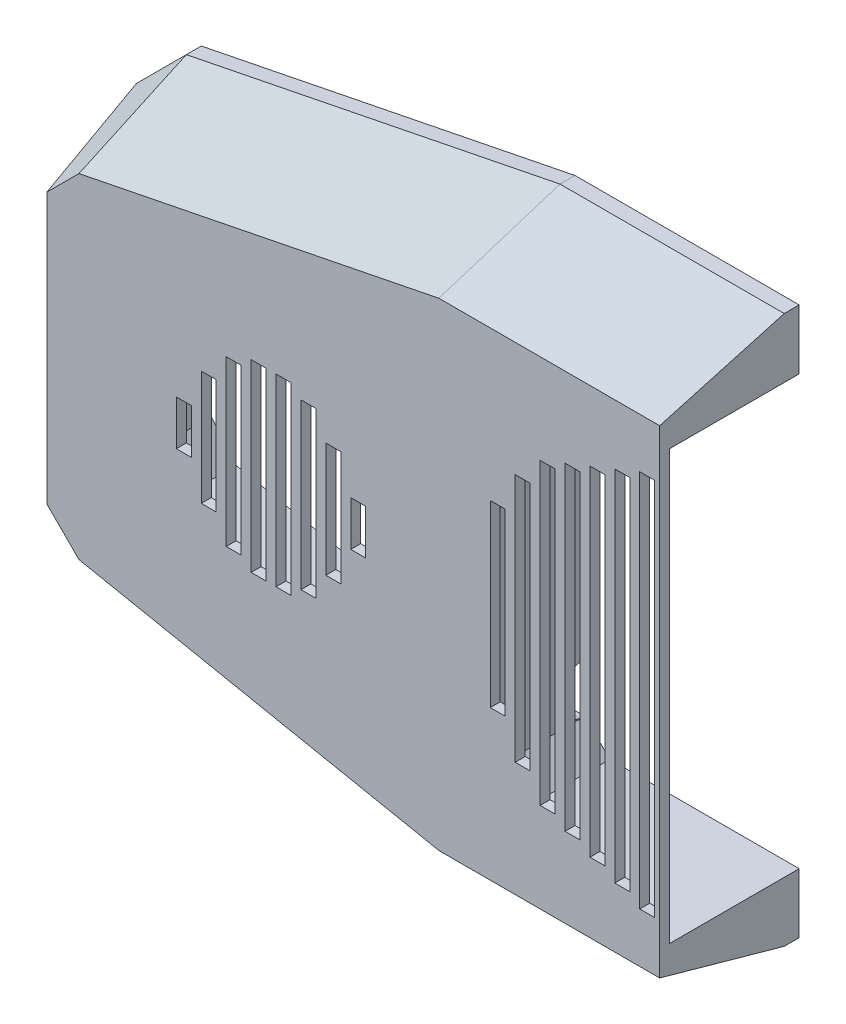
SolidWorks part; units mm, degrees
ref_plane "Plano frontal" through (0, 0, 0) normal (0, 0, 1) x (1, 0, 0)
ref_plane "Plano superior" through (0, 0, 0) normal (0, 1, 0) x (1, 0, 0)
ref_plane "Plano direito" through (0, 0, 0) normal (1, 0, 0) x (0, 0, -1)
sketch "Esboço1" plane through (0, 0, 0) normal (0, 0, 1) x (1, 0, 0)
  line L0 (-120, 30) -> (-45, 45)
  line L1 (-40, 40) -> (40, 40)
  line L2 (-40, 40) -> (-40, -40)
  line L3 (-40, -40) -> (40, -40)
  line L4 (40, 40) -> (40, -40)
  line L6 (-45, 45) -> (-45, 43)
  line L7 (-120, 30) -> (-120, 28)
  line L8 (-40, 30) -> (-40, -30)
  line L9 (-120, -30) -> (-120, -28)
  line L10 (-120, 30) -> (-120, -30)
  line L11 (-45, -43) -> (-120, -28)
  line L12 (40, 30) -> (40, -30)
  line L13 (-120, 28) -> (-45, 43)
  line L14 (120, 30) -> (120, -30)
  line L15 (-45, 45) -> (45, 45)
  line L17 (-45, -45) -> (45, -45)
  line L18 (45, 45) -> (45, -45)
  line L19 (45, -45) -> (45, -43)
  line L21 (-120, -30) -> (-120, 30)
  line L22 (-120, -30) -> (-45, -45)
  line L24 (45, 45) -> (120, 30)
  line L25 (45, -45) -> (120, -30)
  line L27 (-120, -30) -> (-120, 30)
  line L28 (-120, -30) -> (-120, 30)
  line L29 (120, -30) -> (120, -28)
  line L30 (120, 30) -> (120, 28)
  line L31 (45, 45) -> (45, 43)
  line L32 (45, 43) -> (120, 28)
  line L33 (45, -43) -> (120, -28)
  line L36 (120, 30) -> (120, -30)
  line L39 (-45, 45) -> (45, 45)
  line L40 (-45, 45) -> (-45, 43)
  line L41 (-43, 43) -> (43, 43)
  line L42 (45, 45) -> (45, 43)
  line L43 (-45, -45) -> (45, -45)
  line L45 (-43, 43) -> (-43, -43)
  line L46 (45, -45) -> (45, -43)
  line L47 (-45, -43) -> (-43, -43)
  line L48 (-45, -43) -> (-45, 43)
  line L49 (-45, 43) -> (-43, 43)
  line L50 (-43, -43) -> (-43, 43)
  line L51 (45, 43) -> (43, 43)
  line L52 (45, 43) -> (45, -43)
  line L53 (45, -43) -> (43, -43)
  line L54 (43, 43) -> (43, -43)
  line L56 (-43, -43) -> (43, -43)
  line L57 (43, 43) -> (43, -43)
  point P0 (0, 0)
  point P14 (0, 0)
  dimension "D3" = 2
extrude "Ressalto-extrusão3" add sketch "Esboço1" along normal blind 25
sketch "Esboço6" plane through (0, 0, 0) normal (0, 0, 1) x (1, 0, 0)
  line L0 (-120, -28) -> (-120, 28)
  line L1 (-120, 28) -> (-118, 28.4)
  line L2 (-120, 28) -> (-45, 43) construction
  line L3 (-118, 28.4) -> (-118, -28.4)
  line L4 (-45, -43) -> (-120, -28) construction
  line L5 (-118, -28.4) -> (-120, -28)
  line L6 (120, 28) -> (120, -28)
  line L7 (120, -28) -> (118, -28.4)
  line L8 (45, -43) -> (120, -28) construction
  line L9 (118, -28.4) -> (118, 28.4)
  line L10 (118, 28.4) -> (120, 28)
  dimension "D1" = 2
extrude "Ressalto-extrusão16" add sketch "Esboço6" along normal blind 25
sketch "Esboço7" plane through (0, 0, 0) normal (0, 0, 1) x (1, 0, 0)
  line L0 (-120, 40) -> (-45, 55)
  line L1 (-45, -45) -> (45, -45)
  line L2 (-120, -30) -> (-45, -45)
  line L3 (-45, -55) -> (45, -55)
  line L4 (45, 55) -> (120, 40)
  line L5 (120, 30) -> (45, 45)
  line L6 (120, -30) -> (120, 30)
  line L8 (130, -30) -> (130, 30)
  line L9 (-45, 45) -> (45, 45)
  line L11 (-45, 55) -> (45, 55)
  line L13 (45, -55) -> (120, -40)
  line L14 (-120, -30) -> (-120, 30)
  line L15 (-130, -30) -> (-120, -40)
  line L16 (-130, -30) -> (-130, 30)
  line L20 (130, 30) -> (120, 40)
  line L21 (-45, 45) -> (-120, 30)
  line L22 (-120, -40) -> (-45, -55)
  line L23 (-130, 30) -> (-120, 40)
  line L24 (130, -30) -> (120, -40)
  line L25 (120, -30) -> (45, -45)
  dimension "D1" = 10
extrude "Ressalto-extrusão17" add sketch "Esboço7" along normal blind 28
sketch "Esboço8" plane through (0, 0, 0) normal (0, 0, 1) x (1, 0, 0)
  line L0 (-118, 23.4) -> (-113, 29.4)
  line L1 (-118, -28.4) -> (-118, 28.4) construction
  line L2 (-118, 28.4) -> (-45, 43) construction
  line L3 (-113, 29.4) -> (-118, 28.4)
  line L4 (-118, 28.4) -> (-118, 23.4)
  line L5 (-45, 43) -> (-45, 38)
  line L6 (-45, -43) -> (-45, 43) construction
  line L7 (-45, 38) -> (-45, 43)
  line L8 (-45, 43) -> (-45.0847, 42.7932)
  line L9 (-45, 43) -> (-50, 42)
  line L10 (-50, 42) -> (-45, 38)
  line L11 (-45, -43) -> (-45, -38)
  line L12 (-45, -38) -> (-49.9029, -42.0194)
  line L13 (-45, -43) -> (-118, -28.4) construction
  line L14 (-49.9029, -42.0194) -> (-45, -43)
  line L15 (-118, -28.4) -> (-113, -29.4)
  line L16 (-113, -29.4) -> (-118, -23.4)
  line L17 (-118, -23.4) -> (-118, -28.4)
  line L18 (118, 28.4) -> (113, 29.4)
  line L19 (45, 43) -> (118, 28.4) construction
  line L20 (113, 29.4) -> (118, 23.4)
  line L21 (118, 28.4) -> (118, -28.4) construction
  line L22 (118, 23.4) -> (118, 28.4)
  line L23 (118, -28.4) -> (118, -23.4)
  line L24 (118, -23.4) -> (113, -29.4)
  line L25 (45, -43) -> (118, -28.4) construction
  line L26 (113, -29.4) -> (118, -28.4)
  line L27 (45, -43) -> (50, -42)
  line L28 (50, -42) -> (45, -38)
  line L29 (45, 43) -> (45, -43) construction
  line L30 (45, -38) -> (45, -43)
  line L31 (45, 43) -> (50, 42)
  line L32 (50, 42) -> (45, 38)
  line L33 (45, 38) -> (45, 43)
  line L34 (-43, -43) -> (-43, -38)
  line L35 (-43, 43) -> (-43, -43) construction
  line L36 (-43, -38) -> (-38, -43)
  line L37 (-43, -43) -> (43, -43) construction
  line L38 (-38, -43) -> (-43, -43)
  line L39 (-43, 43) -> (-43, 38)
  line L40 (-43, 38) -> (-38, 43)
  line L41 (43, 43) -> (-43, 43) construction
  line L42 (-38, 43) -> (-43, 43)
  line L43 (43, 43) -> (43, 38)
  line L44 (43, 43) -> (43, -43) construction
  line L45 (43, 38) -> (38, 43)
  line L46 (38, 43) -> (43, 43)
  line L47 (43, -43) -> (43, -38)
  line L48 (43, -38) -> (38, -43)
  line L49 (38, -43) -> (43, -43)
  dimension "D1" = 5
  dimension "D2" = 5
  dimension "D3" = 5
  dimension "D4" = 5
  dimension "D5" = 5
  dimension "D6" = 5
  dimension "D7" = 5
  dimension "D8" = 5
  dimension "D9" = 5
  dimension "D10" = 5
  dimension "D11" = 5
  dimension "D12" = 5
  dimension "D13" = 5
  dimension "D14" = 5
  dimension "D15" = 5
  dimension "D16" = 5
  dimension "D17" = 5
  dimension "D18" = 5
  dimension "D19" = 5
  dimension "D20" = 5
  dimension "D21" = 5
  dimension "D22" = 5
  dimension "D23" = 5
  dimension "D24" = 5
chamfer "Chanfro6" distance 25 distance2 7 12 edges at (82.5, 47.5, 28) (125, 35, 28) (130, 0, 28) (125, -35, 28) (82.5, -47.5, 28) (0, -55, 28) (-82.5, -47.5, 28) (-125, -35, 28) (-130, 0, 28) (-125, 35, 28) (-82.5, 47.5, 28) (0, 55, 28)
extrude "Ressalto-extrusão19" add sketch "Esboço8" along normal blind 25
sketch "Esboço9" plane through (0, 0, 0) normal (0, 0, -1) x (-1, 0, 0)
  circle A0 centre (44.1266, -45) radius 1
  circle A1 centre (-44.2337, -45) radius 1
  circle A2 centre (-44.2337, 45) radius 1
  circle A3 centre (44.2337, 45) radius 1
  circle A4 centre (120, -30) radius 1
  circle A5 centre (120, 30) radius 1
  circle A6 centre (-120, 30) radius 1
  circle A7 centre (-120, -30) radius 1
  dimension "D2" = 10
  dimension "D3" = 10
  dimension "D4" = 6.5
  dimension "D5" = 10
  dimension "D6" = 6.5
  dimension "D7" = 10
  dimension "D8" = 6.5
  dimension "D9" = 10
  dimension "D10" = 10
  dimension "D11" = 10
  dimension "D12" = 10
  dimension "D13" = 10
  dimension "D14" = 10
  dimension "D15" = 10
  dimension "D16" = 10
  dimension "D18" = 2
  dimension "D19" = 2
  dimension "D20" = 2
  dimension "D21" = 2
  dimension "D22" = 2
  dimension "D23" = 2
  dimension "D24" = 2
  dimension "D25" = 2
  dimension "D17" = 6.5
extrude "Corte-extrusão1" cut sketch "Esboço9" against normal blind 10
sketch "Esboço10" plane through (0, 0, 25) normal (0, 0, 1) x (1, 0, 0)
  circle A0 centre (117.5, 27.9) radius 1
  circle A1 centre (117.5, -27.9) radius 1.042
  circle A2 centre (-117.5, 27.9) radius 1
  circle A3 centre (-117.5, -27.9) radius 1
  circle A4 centre (44, -42) radius 1
  circle A5 centre (44, 42) radius 1.0492
  circle A6 centre (-44, -42) radius 1
  circle A7 centre (-44, 42) radius 1
  dimension "D1" = 2
  dimension "D2" = 4.5
  dimension "D3" = 4.5
  dimension "D4" = 4.5
  dimension "D5" = 4.5
  dimension "D6" = 2
  dimension "D7" = 4.5
  dimension "D8" = 4.5
  dimension "D9" = 2
  dimension "D10" = 4.5
  dimension "D11" = 4.5
  dimension "D12" = 2
  dimension "D13" = 3
  dimension "D14" = 6
  dimension "D15" = 6
  dimension "D17" = 2
  dimension "D18" = 3
  dimension "D19" = 6
  dimension "D20" = 2
  dimension "D21" = 3
  dimension "D22" = 6
  dimension "D16" = 3
extrude "Corte-extrusão2" [suppressed] cut sketch "Esboço10" against normal blind 10
sketch "Esboço13" plane through (118, 0, 0) normal (-1, 0, 0) x (0, 0, 1)
  line L0 (0, 23.4) -> (0, -23.4) construction
  line L1 (0, 5) -> (5, 5)
  line L2 (0, 5) -> (0, -5)
  line L3 (0, -5) -> (5, -5)
  line L4 (5, 5) -> (5, -5)
  line L5 (25, -23.4) -> (0, -23.4) construction
  line L6 (25, 23.4) -> (23, 23.4)
  line L7 (25, 23.4) -> (25, -23.4)
  line L8 (25, -23.4) -> (23, -23.4)
  line L9 (23, 23.4) -> (23, -23.4)
  line L11 (23, 23.4) -> (20, 23.4)
  line L12 (23, 23.4) -> (23, -23.4)
  line L13 (23, -23.4) -> (20, -23.4)
  line L14 (20, 23.4) -> (20, -23.4)
  line L15 (20, 23.4) -> (18, 23.4)
  line L16 (20, 23.4) -> (20, -23.4)
  line L17 (20, -23.4) -> (18, -23.4)
  line L18 (18, 23.4) -> (18, -23.4)
  line L19 (18, 23.4) -> (15, 23.4)
  line L20 (18, 23.4) -> (18, -23.4)
  line L21 (18, -23.4) -> (15, -23.4)
  line L22 (15, 23.4) -> (15, -23.4)
  line L23 (15, 23.4) -> (13, 23.4)
  line L24 (15, 23.4) -> (15, -23.4)
  line L25 (15, -23.4) -> (13, -23.4)
  line L26 (13, 23.4) -> (13, -23.4)
  line L27 (13, 23.4) -> (10, 23.4)
  line L28 (13, 23.4) -> (13, -23.4)
  line L29 (13, -23.4) -> (10, -23.4)
  line L30 (10, 23.4) -> (10, -23.4)
  line L31 (10, 23.4) -> (8, 23.4)
  line L32 (10, 23.4) -> (10, -23.4)
  line L33 (10, -23.4) -> (8, -23.4)
  line L34 (8, 23.4) -> (8, -23.4)
  line M1 (25, 23.4) -> (0, 23.4)
  line M2 (0, 23.4) -> (0, -23.4)
  line M3 (0, -23.4) -> (25, -23.4)
  dimension "D1" = 5
  dimension "D2" = 10
  dimension "D3" = 18.4
  dimension "D4" = 2
  dimension "D5" = 3
  dimension "D6" = 2
  dimension "D7" = 3
  dimension "D8" = 2
  dimension "D9" = 3
  dimension "D10" = 2
sketch "Esboço14" plane through (-118, 0, 0) normal (1, 0, 0) x (0, 0, -1)
  line L0 (-25, 23.4) -> (0, 23.4) construction
  line L1 (-25, -23.4) -> (-23, -23.4)
  line L2 (-25, -23.4) -> (-25, 23.4)
  line L3 (-25, 23.4) -> (-23, 23.4)
  line L4 (-23, -23.4) -> (-23, 23.4)
  line L6 (-23, -23.4) -> (-20, -23.4)
  line L7 (-23, -23.4) -> (-23, 23.4)
  line L8 (-23, 23.4) -> (-20, 23.4)
  line L9 (-20, -23.4) -> (-20, 23.4)
  line L10 (-20, -23.4) -> (-18, -23.4)
  line L11 (-20, -23.4) -> (-20, 23.4)
  line L12 (-20, 23.4) -> (-18, 23.4)
  line L13 (-18, -23.4) -> (-18, 23.4)
  line L14 (-18, -23.4) -> (-12.5, -23.4)
  line L15 (-18, -23.4) -> (-18, 23.4)
  line L16 (-18, 23.4) -> (-12.5, 23.4)
  line L17 (-18, -23.4) -> (-15, -23.4)
  line L18 (-12.5, -23.4) -> (-10, -23.4)
  line L19 (-18, -23.4) -> (-18, 23.4)
  line L20 (-12.5, 23.4) -> (-10, 23.4)
  line L21 (-10, -23.4) -> (-10, 23.4)
  line L22 (-10, -23.4) -> (-8, -23.4)
  line L23 (-10, -23.4) -> (-10, 23.4)
  line L24 (-10, 23.4) -> (-8, 23.4)
  line L25 (-8, -23.4) -> (-8, 23.4)
  line L26 (-18, 23.4) -> (-15, 23.4)
  line L27 (-15, -23.4) -> (-15, 23.4)
  line L28 (-15, -23.4) -> (-13, -23.4)
  line L29 (-15, -23.4) -> (-15, 23.4)
  line L30 (-15, 23.4) -> (-13, 23.4)
  line L31 (-13, -23.4) -> (-13, 23.4)
  line L32 (-25, -23.4) -> (0, -23.4) construction
  line L33 (-8, 23.4) -> (-5, 23.4)
  line L34 (-8, 23.4) -> (-8, -23.4)
  line L35 (-8, -23.4) -> (-5, -23.4)
  line L36 (-5, 23.4) -> (-5, -23.4)
  line M6 (0, 23.4) -> (-25, 23.4)
  line M8 (-25, -23.4) -> (0, -23.4)
  dimension "D1" = 2
  dimension "D2" = 3
  dimension "D3" = 2
  dimension "D4" = 3
  dimension "D5" = 2
  dimension "D6" = 3
  dimension "D7" = 2
  dimension "D8" = 3
extrude "Corte-extrusão6" cut sketch "Esboço13" against normal through all contours L4 L1 L3 M2 | L14 L9 M1 M3 | L22 L18 M1 M3 | L30 L26 M1 M3
sketch "Esboço15" plane through (43, 0, 0) normal (-1, 0, 0) x (0, 0, 1)
  line L0 (0, 38) -> (0, 33)
  line L1 (0, -38) -> (0, -33)
  line L2 (0, 38) -> (0, 33)
  line L3 (0, 38) -> (0, -38) construction
  line L4 (25, -38) -> (0, -38) construction
  arc A0 (0, 38) -> (0, 33) centre (0, 35.5) cw
  arc A1 (0, -33) -> (0, -38) centre (0, -35.5) cw
  line M3 (0, 38) -> (0, -38)
extrude "Corte-extrusão8" cut sketch "Esboço15" against normal up to next contours A1 M3 | A0 M3
sketch "Esboço16" plane through (-43, 0, 0) normal (1, 0, 0) x (0, 0, -1)
  line L0 (0, -38) -> (0, -28)
  line L1 (0, 38) -> (0, -38) construction
  line L2 (0, 38) -> (0, 28)
  arc A0 (0, -38) -> (0, -28) centre (0, -33) cw
  arc A1 (0, 28) -> (0, 38) centre (0, 33) cw
  line M2 (0, -38) -> (0, 38)
  dimension "D1" = 10
  dimension "D2" = 10
extrude "Corte-extrusão9" cut sketch "Esboço16" against normal up to next contours A0 M2 | A1 M2
extrude "Corte-extrusão10" cut sketch "Esboço14" against normal up to next contours L9 L4 M8 M6 | L27 L16 L13 M8 | L31 L21 M8 M6 | L36 L25 M6 M8
sketch "Esboço20" plane through (0, 0, 28) normal (0, 0, 1) x (1, 0, 0)
  line L0 (-120, 30) -> (-45, 45)
  line L1 (-45, 45) -> (45, 45)
  line L2 (45, 45) -> (120, 30)
  line L3 (120, 30) -> (120, -30)
  line L4 (120, -30) -> (45, -45)
  line L5 (45, -45) -> (-45, -45)
  line L6 (-45, -45) -> (-120, -30)
  line L7 (-120, -30) -> (-120, 30)
extrude "Ressalto-extrusão20" add sketch "Esboço20" against normal blind 3
sketch "Esboço21" plane through (0, 0, 25) normal (0, 0, -1) x (-1, 0, 0)
  circle A0 centre (0, 0) radius 40
  dimension "D1" = 80
sketch "Esboço22" plane through (0, 0, 25) normal (0, 0, -1) x (-1, 0, 0)
  line L0 (38, -43) -> (-38, -43) construction
  line L1 (-1, -39) -> (1, -39)
  line L2 (-1, -39) -> (-1, 39)
  line L3 (-1, 39) -> (1, 39)
  line L4 (1, -39) -> (1, 39)
  line L5 (-1, -39) -> (1, 39) construction
  line L6 (-1, 39) -> (1, -39) construction
  line L7 (-1, -38) -> (-4, -38)
  line L8 (-1, -38) -> (-1, 38)
  line L9 (-1, 38) -> (-4, 38)
  line L10 (-4, -38) -> (-4, 38)
  line L11 (-4, -37) -> (-6, -37)
  line L12 (-4, -37) -> (-4, 37)
  line L13 (-4, 37) -> (-6, 37)
  line L14 (-6, -37) -> (-6, 37)
  line L17 (-6, -36) -> (-9, -36)
  line L18 (-6, -36) -> (-6, 36)
  line L19 (-6, 36) -> (-9, 36)
  line L20 (-9, -36) -> (-9, 36)
  line L21 (-9, -35) -> (-11, -35)
  line L22 (-9, -35) -> (-9, 35)
  line L23 (-9, 35) -> (-11, 35)
  line L24 (-11, -35) -> (-11, 35)
  line L25 (-11, -34) -> (-14, -34)
  line L26 (-11, -34) -> (-11, 34)
  line L27 (-11, 34) -> (-14, 34)
  line L28 (-14, -34) -> (-14, 34)
  line L29 (-14, -33) -> (-16, -33)
  line L30 (-14, -33) -> (-14, 33)
  line L31 (-14, 33) -> (-16, 33)
  line L32 (-16, -33) -> (-16, 33)
  line L33 (-16, -32) -> (-19, -32)
  line L34 (-16, -32) -> (-16, 32)
  line L35 (-16, 32) -> (-19, 32)
  line L36 (-19, -32) -> (-19, 32)
  line L37 (-19, -31) -> (-21, -31)
  line L38 (-19, -31) -> (-19, 31)
  line L39 (-19, 31) -> (-21, 31)
  line L40 (-21, -31) -> (-21, 31)
  line L41 (-21, -30) -> (-24, -30)
  line L42 (-21, -30) -> (-21, 30)
  line L43 (-21, 30) -> (-24, 30)
  line L44 (-24, -30) -> (-24, 30)
  line L45 (-24, -28) -> (-25.7991, -28)
  line L46 (-24, -28) -> (-24, 28)
  line L47 (-24, 28) -> (-25.7991, 28)
  line L48 (-25.7991, -28) -> (-25.7991, 28)
  line L49 (-25.7991, -25) -> (-28.7991, -25)
  line L50 (-25.7991, -25) -> (-25.7991, 25)
  line L51 (-25.7991, 25) -> (-28.7991, 25)
  line L52 (-28.7991, -25) -> (-28.7991, 25)
  line L53 (-28.7991, -22) -> (-30.7991, -22)
  line L54 (-28.7991, -22) -> (-28.7991, 22)
  line L55 (-28.7991, 22) -> (-30.7991, 22)
  line L56 (-30.7991, -22) -> (-30.7991, 22)
  line L57 (-30.7991, -18) -> (-33.7991, -18)
  line L58 (-30.7991, -18) -> (-30.7991, 18)
  line L59 (-30.7991, 18) -> (-33.7991, 18)
  line L60 (-33.7991, -18) -> (-33.7991, 18)
  line L61 (-33.7991, -14) -> (-35.7991, -14)
  line L62 (-33.7991, -14) -> (-33.7991, 14)
  line L63 (-33.7991, 14) -> (-35.7991, 14)
  line L64 (-35.7991, -14) -> (-35.7991, 14)
  line L65 (1, -38) -> (4, -38)
  line L66 (1, -38) -> (1, 38)
  line L67 (1, 38) -> (4, 38)
  line L68 (4, -38) -> (4, 38)
  line L69 (4, -37) -> (6, -37)
  line L70 (4, -37) -> (4, 37)
  line L71 (4, 37) -> (6, 37)
  line L72 (6, -37) -> (6, 37)
  line L73 (6, -36) -> (9, -36)
  line L74 (6, -36) -> (6, 36)
  line L75 (6, 36) -> (9, 36)
  line L76 (9, -36) -> (9, 36)
  line L77 (9, -35) -> (11, -35)
  line L78 (9, -35) -> (9, 35)
  line L79 (9, 35) -> (11, 35)
  line L80 (11, -35) -> (11, 35)
  line L81 (11, -34) -> (14, -34)
  line L82 (11, -34) -> (11, 34)
  line L83 (11, 34) -> (14, 34)
  line L84 (14, -34) -> (14, 34)
  line L85 (14, -33) -> (16, -33)
  line L86 (14, -33) -> (14, 33)
  line L87 (14, 33) -> (16, 33)
  line L88 (16, -33) -> (16, 33)
  line L89 (16, -32) -> (19, -32)
  line L90 (16, -32) -> (16, 32)
  line L91 (16, 32) -> (19, 32)
  line L92 (19, -32) -> (19, 32)
  line L93 (19, -31) -> (21, -31)
  line L94 (19, -31) -> (19, 31)
  line L95 (19, 31) -> (21, 31)
  line L96 (21, -31) -> (21, 31)
  line L97 (21, -30) -> (24, -30)
  line L98 (21, -30) -> (21, 30)
  line L99 (21, 30) -> (24, 30)
  line L100 (24, -30) -> (24, 30)
  line L101 (24, -28) -> (26, -28)
  line L102 (24, -28) -> (24, 28)
  line L103 (24, 28) -> (26, 28)
  line L104 (26, -28) -> (26, 28)
  line L105 (26, -25) -> (29, -25)
  line L106 (26, -25) -> (26, 25)
  line L107 (26, 25) -> (29, 25)
  line L108 (29, -25) -> (29, 25)
  line L109 (29, -22) -> (31, -22)
  line L110 (29, -22) -> (29, 22.9327)
  line L111 (29, 22.9327) -> (31, 22.9327)
  line L112 (31, -22) -> (31, 22.9327)
  line L113 (31, -18) -> (34, -18)
  line L114 (31, -18) -> (31, 18)
  line L115 (31, 18) -> (34, 18)
  line L116 (34, -18) -> (34, 18)
  line L117 (34, -14) -> (36, -14)
  line L118 (34, -14) -> (34, 14)
  line L119 (34, 14) -> (36, 14)
  line L120 (36, -14) -> (36, 14)
  point P0 (0, 0)
  dimension "D1" = 2
  dimension "D2" = 3
  dimension "D3" = 2
  dimension "D4" = 4
  dimension "D5" = 1
  dimension "D6" = 1
  dimension "D7" = 1
  dimension "D8" = 1
  dimension "D9" = 3
  dimension "D10" = 2
  dimension "D11" = 3
  dimension "D12" = 2
  dimension "D13" = 3
  dimension "D14" = 1
  dimension "D15" = 1
  dimension "D16" = 1
  dimension "D17" = 1
  dimension "D18" = 1
  dimension "D19" = 1
  dimension "D20" = 1
  dimension "D21" = 1
  dimension "D22" = 1
  dimension "D23" = 1
  dimension "D24" = 1
  dimension "D25" = 1
  dimension "D26" = 2
  dimension "D27" = 3
  dimension "D28" = 3
  dimension "D29" = 4
  dimension "D30" = 1
  dimension "D31" = 1
  dimension "D32" = 2
  dimension "D33" = 3
  dimension "D34" = 3
  dimension "D35" = 4
  dimension "D36" = 2
  dimension "D37" = 3
  dimension "D38" = 3
  dimension "D39" = 2
  dimension "D40" = 3
  dimension "D41" = 2
  dimension "D42" = 4
  dimension "D43" = 3
  dimension "D44" = 4
  dimension "D45" = 2
  dimension "D46" = 3
  dimension "D47" = 2
  dimension "D48" = 3
  dimension "D49" = 2
  dimension "D50" = 3
  dimension "D51" = 2
  dimension "D52" = 3
  dimension "D53" = 2
  dimension "D54" = 3
  dimension "D55" = 2
  dimension "D56" = 3
  dimension "D57" = 2
extrude "Corte-extrusão13" cut sketch "Esboço22" against normal blind 3 contours L60 L57 L56 L59 | L52 L49 L48 L51 | L44 L41 L40 L43 | L36 L33 L32 L35 | L28 L25 L24 L27 | L20 L17 L14 L19 | L10 L7 L2 L9 | L65 L68 L67 L4 | L73 L76 L75 L72 | L81 L84 L83 L80 | L89 L92 L91 L88 | L97 L100 L99 L96 | L105 L108 L107 L104 | L113 L116 L115 L112
sketch "Esboço23" plane through (0, 0, 25) normal (0, 0, -1) x (-1, 0, 0)
  line L0 (45, 0) -> (118, 0)
  line L1 (45, -38) -> (45, 38) construction
  line L2 (118, -23.4) -> (118, 23.4) construction
  line L3 (-45, 0) -> (-118, 0)
  line L4 (-45, 38) -> (-45, -38) construction
  line L5 (-118, 23.4) -> (-118, -23.4) construction
  line L7 (-77, 18.5) -> (-79, 18.5)
  line L8 (-77, 18.5) -> (-77, -18.5)
  line L9 (-77, -18.5) -> (-79, -18.5)
  line L10 (-79, 18.5) -> (-79, -18.5)
  line L11 (-77, 18.5) -> (-79, -18.5) construction
  line L12 (-77, -18.5) -> (-79, 18.5) construction
  line L13 (-55.1028, 22.5) -> (-100.1028, 22.5)
  line L14 (-55.1028, 22.5) -> (-55.1028, -22.5)
  line L15 (-55.1028, -22.5) -> (-100.1028, -22.5)
  line L16 (-100.1028, 22.5) -> (-100.1028, -22.5)
  line L17 (-69, 14.5) -> (-67, 14.5)
  line L18 (-69, 14.5) -> (-69, -14.5)
  line L19 (-77, 18.5) -> (-74, 18.5)
  line L20 (-77, 18.5) -> (-77, -18.5)
  line L21 (-77, -18.5) -> (-74, -18.5)
  line L22 (-74, 18.5) -> (-74, -18.5)
  line L23 (-74, 17.5) -> (-72, 17.5)
  line L24 (-74, 17.5) -> (-74, -17.5)
  line L25 (-74, -17.5) -> (-72, -17.5)
  line L26 (-72, 17.5) -> (-72, -17.5)
  line L27 (-72, 16.5) -> (-69, 16.5)
  line L28 (-72, 16.5) -> (-72, -16.5)
  line L29 (-72, -16.5) -> (-69, -16.5)
  line L30 (-69, 16.5) -> (-69, -16.5)
  line L31 (-69, -14.5) -> (-67, -14.5)
  line L32 (-67, 14.5) -> (-67, -14.5)
  line L33 (-67, 11.5) -> (-64, 11.5)
  line L34 (-67, 11.5) -> (-67, -11.5)
  line L35 (-67, -11.5) -> (-64, -11.5)
  line L36 (-64, 11.5) -> (-64, -11.5)
  line L37 (-64, 8.5) -> (-62, 8.5)
  line L38 (-64, 8.5) -> (-64, -8.5)
  line L39 (-64, -8.5) -> (-62, -8.5)
  line L40 (-62, 8.5) -> (-62, -8.5)
  line L41 (-62, -4.5) -> (-59, -4.5)
  line L42 (-62, -4.5) -> (-62, 4.5)
  line L43 (-62, 4.5) -> (-59, 4.5)
  line L44 (-59, -4.5) -> (-59, 4.5)
  line L45 (-79, 18.5) -> (-82, 18.5)
  line L46 (-79, 18.5) -> (-79, -18.5)
  line L47 (-79, -18.5) -> (-82, -18.5)
  line L48 (-82, 18.5) -> (-82, -18.5)
  line L49 (-82, 17.5) -> (-84, 17.5)
  line L50 (-82, 17.5) -> (-82, -17.5)
  line L51 (-82, -17.5) -> (-84, -17.5)
  line L52 (-84, 17.5) -> (-84, -17.5)
  line L53 (-84, 16.5) -> (-87, 16.5)
  line L54 (-84, 16.5) -> (-84, -16.5)
  line L55 (-84, -16.5) -> (-87, -16.5)
  line L56 (-87, 16.5) -> (-87, -16.5)
  line L57 (-87, 14.5) -> (-89, 14.5)
  line L58 (-87, 14.5) -> (-87, -14.5)
  line L59 (-87, -14.5) -> (-89, -14.5)
  line L60 (-89, 14.5) -> (-89, -14.5)
  line L61 (-89, 11.5) -> (-92, 11.5)
  line L62 (-89, 11.5) -> (-89, -11.5)
  line L63 (-89, -11.5) -> (-92, -11.5)
  line L64 (-92, 11.5) -> (-92, -11.5)
  line L65 (-92, 8.5) -> (-94, 8.5)
  line L66 (-92, 8.5) -> (-92, -8.5)
  line L67 (-92, -8.5) -> (-94, -8.5)
  line L68 (-94, 8.5) -> (-94, -8.5)
  line L69 (-94, 4.5) -> (-97, 4.5)
  line L70 (-94, 4.5) -> (-94, -4.5)
  line L71 (-94, -4.5) -> (-97, -4.5)
  line L72 (-97, 4.5) -> (-97, -4.5)
  line L73 (77, 18.5) -> (79, 18.5)
  line L74 (77, 18.5) -> (77, -18.5)
  line L75 (77, -18.5) -> (79, -18.5)
  line L76 (79, 18.5) -> (79, -18.5)
  line L77 (77, 18.5) -> (79, -18.5) construction
  line L78 (77, -18.5) -> (79, 18.5) construction
  line L79 (77, 18.5) -> (74, 18.5)
  line L80 (77, 18.5) -> (77, -18.5)
  line L81 (77, -18.5) -> (74, -18.5)
  line L82 (74, 18.5) -> (74, -18.5)
  line L83 (79, -18.5) -> (82, -18.5)
  line L84 (79, -18.5) -> (79, 18.5)
  line L85 (79, 18.5) -> (82, 18.5)
  line L86 (82, -18.5) -> (82, 18.5)
  line L87 (74, 17.5) -> (72, 17.5)
  line L88 (74, 17.5) -> (74, -17.5)
  line L89 (74, -17.5) -> (72, -17.5)
  line L90 (72, 17.5) -> (72, -17.5)
  line L91 (72, 16.5) -> (69, 16.5)
  line L92 (72, 16.5) -> (72, -16.5)
  line L93 (72, -16.5) -> (69, -16.5)
  line L94 (69, 16.5) -> (69, -16.5)
  line L95 (69, 14.5) -> (67, 14.5)
  line L96 (69, 14.5) -> (69, -14.5)
  line L97 (69, -14.5) -> (67, -14.5)
  line L98 (67, 14.5) -> (67, -14.5)
  line L99 (67, 11.5) -> (64, 11.5)
  line L100 (67, 11.5) -> (67, -11.5)
  line L101 (67, -11.5) -> (64, -11.5)
  line L102 (64, 11.5) -> (64, -11.5)
  line L103 (64, 8.5) -> (62, 8.5)
  line L104 (64, 8.5) -> (64, -8.5)
  line L105 (64, -8.5) -> (62, -8.5)
  line L106 (62, 8.5) -> (62, -8.5)
  line L107 (62, 4.5) -> (59, 4.5)
  line L108 (62, 4.5) -> (62, -4.5)
  line L109 (62, -4.5) -> (59, -4.5)
  line L110 (59, 4.5) -> (59, -4.5)
  line L111 (82, 17.5) -> (84, 17.5)
  line L112 (82, 17.5) -> (82, -17.5)
  line L113 (82, -17.5) -> (84, -17.5)
  line L114 (84, 17.5) -> (84, -17.5)
  line L115 (84, 16.5) -> (87, 16.5)
  line L116 (84, 16.5) -> (84, -16.5)
  line L117 (84, -16.5) -> (87, -16.5)
  line L118 (87, 16.5) -> (87, -16.5)
  line L119 (87, 14.5) -> (89, 14.5)
  line L120 (87, 14.5) -> (87, -14.5)
  line L121 (87, -14.5) -> (89, -14.5)
  line L122 (89, 14.5) -> (89, -14.5)
  line L123 (89, 11.5) -> (92, 11.5)
  line L124 (89, 11.5) -> (89, -11.5)
  line L125 (89, -11.5) -> (92, -11.5)
  line L126 (92, 11.5) -> (92, -11.5)
  line L127 (92, 8.5) -> (94, 8.5)
  line L128 (92, 8.5) -> (92, -8.5)
  line L129 (92, -8.5) -> (94, -8.5)
  line L130 (94, 8.5) -> (94, -8.5)
  line L131 (94, 4.5) -> (97, 4.5)
  line L132 (94, 4.5) -> (94, -4.5)
  line L133 (94, -4.5) -> (97, -4.5)
  line L134 (97, 4.5) -> (97, -4.5)
  circle A0 centre (78, 0) radius 20
  circle A1 centre (-78, 0) radius 20
  dimension "D1" = 40
  dimension "D3" = 40
  dimension "D2" = 40
  dimension "D4" = 40
  dimension "D5" = 45
  dimension "D6" = 45
  dimension "D7" = 4
  dimension "D8" = 4
  dimension "D9" = 2
  dimension "D10" = 3
  dimension "D11" = 2
  dimension "D12" = 3
  dimension "D13" = 1
  dimension "D14" = 1
  dimension "D15" = 2
  dimension "D16" = 3
  dimension "D17" = 2
  dimension "D18" = 3
  dimension "D19" = 2
  dimension "D20" = 3
  dimension "D21" = 3
  dimension "D22" = 4
  dimension "D23" = 4
  dimension "D24" = 3
  dimension "D25" = 3
  dimension "D26" = 1
  dimension "D27" = 1
  dimension "D28" = 2
  dimension "D29" = 3
  dimension "D30" = 2
  dimension "D31" = 3
  dimension "D32" = 2
  dimension "D33" = 3
  dimension "D34" = 2
  dimension "D35" = 3
  dimension "D36" = 2
  dimension "D37" = 3
  dimension "D38" = 3
  dimension "D39" = 2
  dimension "D40" = 2
  dimension "D41" = 3
  dimension "D42" = 3
  dimension "D43" = 2
  dimension "D44" = 3
  dimension "D45" = 2
  dimension "D46" = 3
  dimension "D47" = 2
  dimension "D48" = 3
  dimension "D49" = 2
  dimension "D50" = 3
extrude "Corte-extrusão14" cut sketch "Esboço23" against normal blind 3 contours L41 L44 L3 L40 | L3 L44 L43 L40 | L36 L33 L32 L3 | L36 L3 L32 L35 | L30 L27 L26 L3 L18 | L30 L18 L3 L26 L29 | L22 L3 L8 L21 | L22 L19 L8 L3 | L45 L48 L3 L10 | L3 L48 L47 L10 | L3 L56 L55 L52 | L53 L56 L3 L52 | L61 L64 L3 L60 | L3 L64 L63 L60 | L69 L72 L3 L68 | L3 L72 L71 L68 | L107 L110 L0 L106 | L0 L110 L109 L106 | L99 L102 L0 L98 | L0 L102 L101 L98 | L91 L94 L0 L90 | L0 L94 L93 L90 | L0 L82 L81 L74 | L79 L82 L0 L74 | L0 L86 L85 L76 | L83 L86 L0 L76 | L118 L115 L114 L0 | L118 L0 L114 L117 | L126 L0 L122 L125 | L134 L0 L130 L133 | L134 L131 L130 L0 | L126 L123 L122 L0
sketch "Esboço24" plane through (0, 0, 0) normal (0, 0, -1) x (-1, 0, 0)
  line L0 (-45, 55) -> (45, 55) construction
  line L1 (0, 55) -> (-130, 55)
  line L2 (0, 55) -> (0, -55)
  line L3 (0, -55) -> (-130, -55)
  line L4 (-130, 55) -> (-130, -55)
extrude "Corte-extrusão15" cut sketch "Esboço24" against normal up to next
sketch "Esboço25" plane through (0, 0, 25) normal (0, 0, -1) x (-1, 0, 0)
  line L0 (0, -43) -> (38, -43)
  line L1 (38, -43) -> (43, -38)
  line L2 (43, -38) -> (43, 38)
  line L3 (43, 38) -> (38, 43)
  line L4 (38, 43) -> (0, 43)
  line L5 (0, 43) -> (0, -43)
extrude "Corte-extrusão16" cut sketch "Esboço25" against normal blind 1
sketch "Esboço26" plane through (0, 0, 25) normal (0, 0, -1) x (-1, 0, 0)
  line L0 (45, 38) -> (50, 42)
  line L1 (50, 42) -> (113, 29.4)
  line L2 (113, 29.4) -> (118, 23.4)
  line L3 (118, 23.4) -> (118, -23.4)
  line L4 (118, -23.4) -> (113, -29.4)
  line L5 (113, -29.4) -> (49.9029, -42.0194)
  line L6 (49.9029, -42.0194) -> (45, -38)
  line L7 (45, -38) -> (45, 38)
  line L8 (45, 38) -> (45.9365, 37.7451)
extrude "Corte-extrusão17" cut sketch "Esboço26" against normal blind 1
